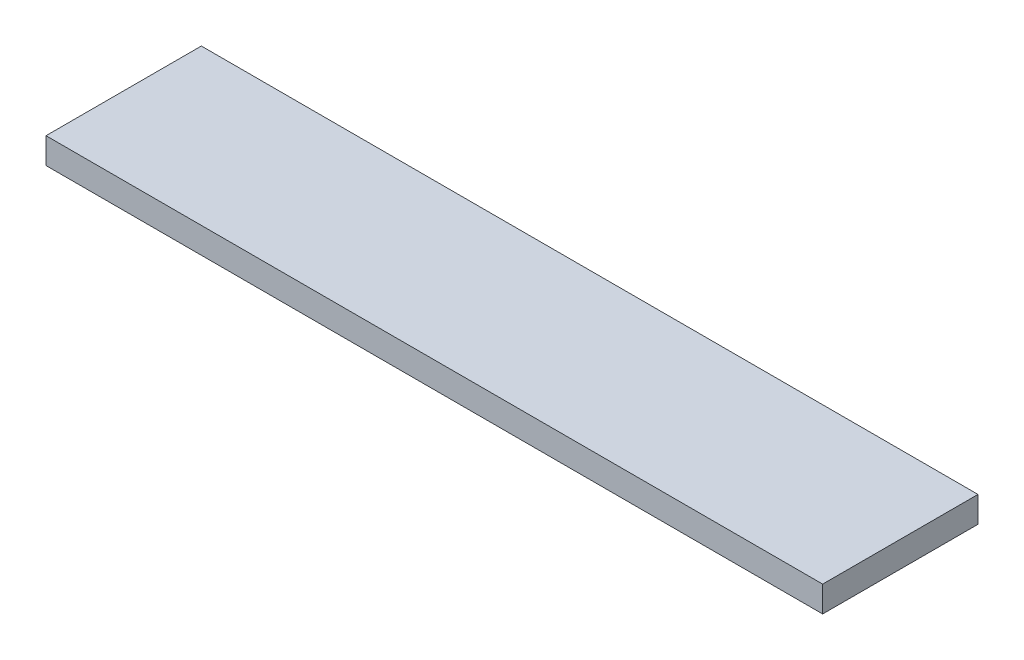
SolidWorks part; units mm, degrees
material "1060 Alloy"
ref_plane "Front Plane" through (0, 0, 0) normal (0, 0, 1) x (1, 0, 0)
ref_plane "Top Plane" through (0, 0, 0) normal (0, 1, 0) x (1, 0, 0)
ref_plane "Right Plane" through (0, 0, 0) normal (1, 0, 0) x (0, 0, -1)
sketch "Sketch1" plane through (0, 0, 0) normal (0, 1, 0) x (1, 0, 0)
  line L1 (-95.25, 19.05) -> (95.25, 19.05)
  line L2 (-95.25, 19.05) -> (-95.25, -19.05)
  line L3 (-95.25, -19.05) -> (95.25, -19.05)
  line L4 (95.25, 19.05) -> (95.25, -19.05)
  line L5 (-95.25, 19.05) -> (95.25, -19.05) construction
  line L6 (-95.25, -19.05) -> (95.25, 19.05) construction
  point P0 (0, 0)
  dimension "D1" = 190.5
  dimension "D2" = 38.1
extrude "Boss-Extrude1" add sketch "Sketch1" along normal blind 6.35
